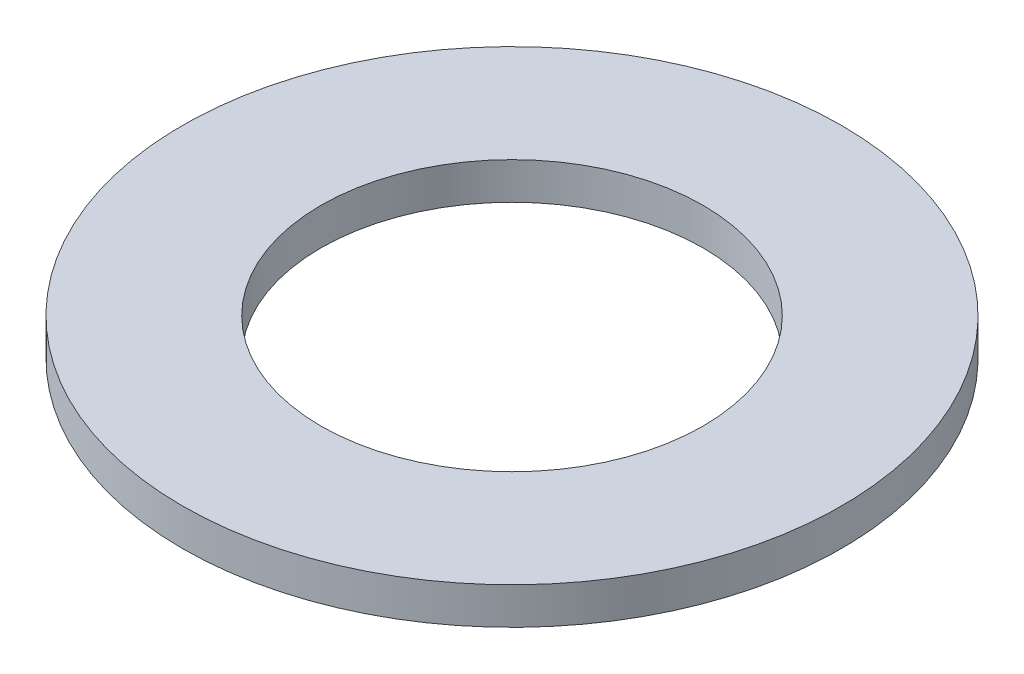
SolidWorks part; units mm, degrees
material "Alloy Steel"
ref_plane "Front Plane" through (0, 0, 0) normal (0, 0, 1) x (1, 0, 0)
ref_plane "Top Plane" through (0, 0, 0) normal (0, 1, 0) x (1, 0, 0)
ref_plane "Right Plane" through (0, 0, 0) normal (1, 0, 0) x (0, 0, -1)
sketch "Sketch1" plane through (0, 0, 0) normal (0, 1, 0) x (1, 0, 0)
  circle A0 centre (0, 0) radius 22.225
  dimension "OD" = 44.45
extrude "Boss-Extrude1" add sketch "Sketch1" along normal blind 2.4892
sketch "Sketch5" plane through (0, 2.4892, 0) normal (0, 1, 0) x (-1, 0, 0)
  circle A0 centre (0, 0) radius 12.8905
  dimension "ID" = 25.781
extrude "Cut-Extrude1" cut sketch "Sketch5" against normal through all
